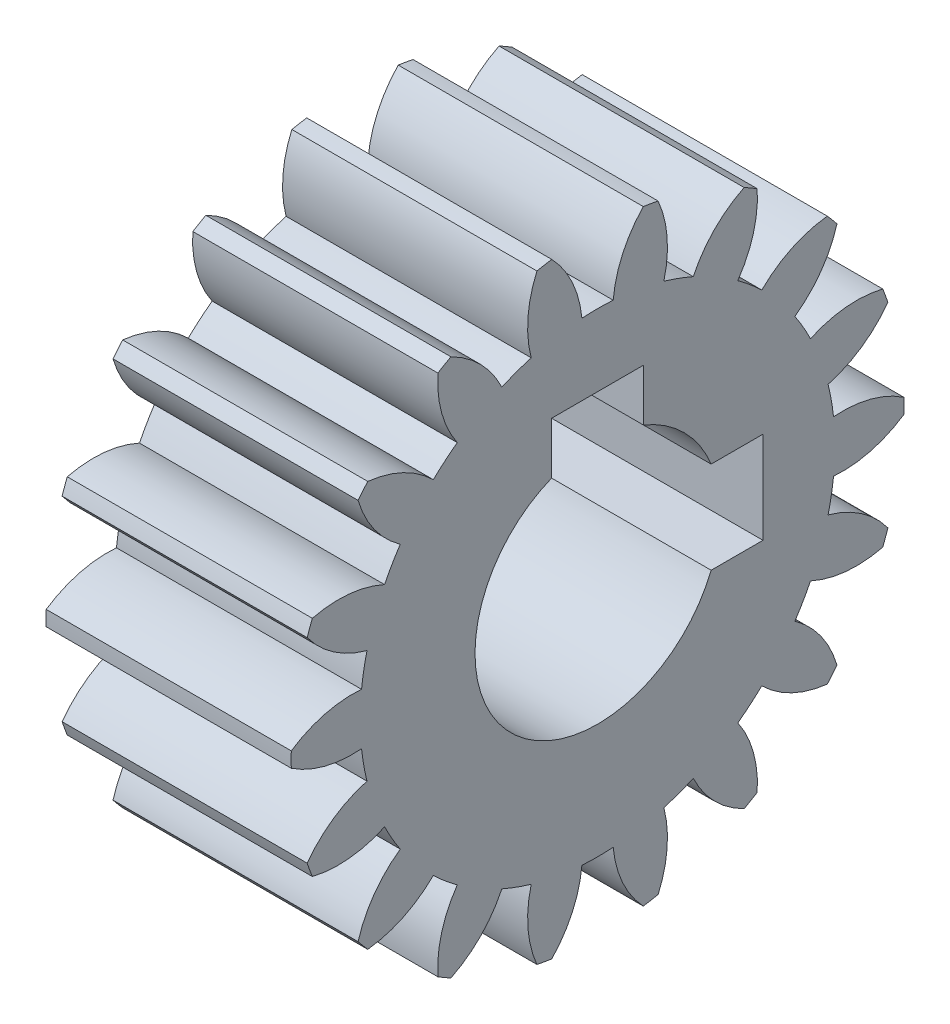
SolidWorks part; units mm, degrees
ref_plane "Plane1" through (0, 0, 0) normal (0, 0, 1) x (1, 0, 0)
ref_plane "Plane2" through (0, 0, 0) normal (0, 1, 0) x (1, 0, 0)
ref_plane "Plane3" through (0, 0, 0) normal (1, 0, 0) x (0, 0, -1)
sketch "HoldingSke" plane through (0, 0, 0) normal (0, 1, 0) x (1, 0, 0)
  line L0 (0, 0) -> (0.9511, -0.309)
  line L1 (-15, 0) -> (100, 0) construction
  line L2 (0, 0) -> (-2.1039, 2.3779)
  line L3 (0, 0) -> (-11.863, 4.5341)
  line L4 (0, 0) -> (8.2133, 2.6687)
  line L5 (0, 0) -> (-46.8476, -17.4728)
  line L6 (0, 0) -> (-6.6317, -4.4744)
  line L7 (-2.1039, 2.3779) -> (8.6586, 51.2059)
  line L8 (-76.2, 54.61) -> (-74.8, 54.61)
  line L9 (-71.009, 38.7566) -> (-53.1078, 45.2721)
  line L10 (-76.2, 71.12) -> (104.1128, 71.12)
  line L11 (0, 0) -> (-8, 0)
  line L12 (-76.2, 101.6) -> (-76.162, 101.6)
  line L13 (24.9733, 27.94) -> (52.9518, 28.4284)
  line L14 (24.9733, 27.94) -> (24.9743, 27.94)
  line L15 (24.9733, 27.94) -> (100.4006, 29.5858)
  line L16 (-63.627, -1) -> (-12.827, -1)
  circle A0 centre (0, 0) radius 4
  circle A1 centre (0, 0) radius 7.749
  circle A2 centre (0, 0) radius 37.5
  circle A3 centre (0, 0) radius 4
  dimension "MHD" = 15.498
  dimension "Hub_dia" = 75
  dimension "Bore" = 8
  dimension "MBD" = 8
  dimension "Num_teeth" = 18
  dimension "Pitch" = 1
  dimension "Overall_len" = 50
  dimension "Show_teeth" = 18
  dimension "Thickness" = 8
  dimension "OAL" = 50.0001
  dimension "T_dim" = 1.4
  dimension "Ap" = 20
  dimension "H" = 19.05
  dimension "Pitch_radius" = 180.3128
  dimension "Width" = 8
  dimension "Backlash" = 0.038
  dimension "Addendum_fac" = 1
  dimension "Dedendum_fac" = 1.25
  dimension "Clearance_fac" = 0.25
  dimension "Dedendum_add" = 0.001
  dimension "Module" = 1
sketch "BasProSke" plane through (0, 0, 0) normal (0, 1, 0) x (1, 0, 0)
  line L0 (-10, 0) -> (60, 0) construction
  line L1 (0, 0) -> (0, 10)
  line L2 (0, 0) -> (8, 0)
  line L3 (8, 0) -> (8, 10)
  line L4 (8, 10) -> (0, 10)
  dimension "Thickness" = 8
  dimension "Diameter" = 20
revolve "Base-Revolve" add sketch "BasProSke" angle 360 about L0
sketch "TooCutSke" plane through (0, 0, 0) normal (1, 0, 0) x (0, 0, -1)
  line L1 (0, 0) -> (0, 107) construction
  line L2 (0, 0) -> (-0.8509, 8.9597) construction
  line L3 (0, 0) -> (-3.1157, 17.6701) construction
  line L4 (-0.8509, 8.9597) -> (-1.5579, 8.835) construction
  arc A0 (0.5106, 7.7322) -> (-0.5106, 7.7322) centre (0, 0) ccw
  arc A1 (1.5152, 9.9102) -> (-1.5152, 9.9102) centre (0, 0) ccw
  circle A2 centre (0, 0) radius 9 construction
  circle A3 centre (0, 0) radius 8.4572 construction
  arc A4 (-0.5106, 7.7322) -> (-1.5152, 9.9102) centre (-4.0952, 7.3996) ccw
  arc A5 (1.5152, 9.9102) -> (0.5106, 7.7322) centre (4.0952, 7.3996) ccw
  dimension "Root_dia" = 15.498
  dimension "Overcut_dia" = 20.0508
  dimension "Pitch_dia" = 18
  dimension "Base_dia" = 16.9145
  dimension "Flank_rad" = 3.6
  dimension "Half_ang" = 10
  dimension "Half_CT" = 0.7179
extrude "ToothCut" cut sketch "TooCutSke" along normal through all
fillet "Breaks" [suppressed] radius 0.02
fillet "RootFillets" [suppressed] radius 0.251
pattern_circular "TeethCuts" count 18 every 20 about axis through (-10, 0, 0) along (1, 0, 0) of "ToothCut", "RootFillets", "Breaks"
sketch "HubNeaOneSke" plane through (0, 0, 0) normal (-1, 0, 0) x (0, 0, 1)
  circle A0 centre (0, 0) radius 7.749
  dimension "Diameter" = 15.498
extrude "HubNearOne" [suppressed] add sketch "HubNeaOneSke" along normal blind 42.0001
sketch "HubNeaBotSke" plane through (0, 0, 0) normal (-1, 0, 0) x (0, 0, 1)
  circle A0 centre (0, 0) radius 7.749
  dimension "Diameter" = 15.498
extrude "HubNearBoth" [suppressed] add sketch "HubNeaBotSke" along normal blind 21
ref_plane "FarPln" through (8, 0, 0) normal (1, 0, 0) x (0, 0, -1)
sketch "HubFarSke" plane through (8, 0, 0) normal (1, 0, 0) x (0, 0, -1)
  circle A0 centre (0, 0) radius 7.749
  dimension "Diameter" = 15.498
extrude "HubFar" [suppressed] add sketch "HubFarSke" along normal blind 21
sketch "BorSke" plane through (0, 0, 0) normal (1, 0, 0) x (0, 0, -1)
  circle A0 centre (0, 0) radius 4
  dimension "Diameter" = 8
extrude "Bore" cut sketch "BorSke" along normal mid plane 100.0001
sketch "KeySke" plane through (0, 0, 0) normal (1, 0, 0) x (0, 0, -1)
  line L0 (-1.5, 0) -> (-1.5, 5.4)
  line L1 (-1.5, 5.4) -> (1.5, 5.4)
  line L2 (1.5, 5.4) -> (1.5, 0)
  line L3 (0, 0) -> (0, 34) construction
  line L4 (-1.5, 0) -> (1.5, 0)
  dimension "Offset" = 5.4
  dimension "Width" = 3
extrude "Keyway" cut sketch "KeySke" along normal mid plane 100.0001
pattern_circular "Keyway2" count 2 every 90 about axis through (0, 0, 0) along (1, 0, 0) of "Keyway"
ref_plane "基准面1" through (4, 0, 0) normal (1, 0, 0) x (0, 0, -1)
sketch "草图1" plane through (4, 0, 0) normal (1, 0, 0) x (0, 0, -1)
  line L0 (0, 0) -> (4.981, 5.9361)
  line L1 (0, 0) -> (-4.981, 5.9361)
ref_plane "基准面2" through (0, 0, 0) normal (0, -0.6428, -0.766) x (-1, 0, 0)
ref_plane "基准面3" through (0, 0, 0) normal (0, 0.6428, -0.766) x (-1, 0, 0)
equation "' \"Module@HoldingSke\" = 6.35"
equation "' \"Num_teeth@HoldingSke\" = 12"
equation "' \"Ap@HoldingSke\" =  20"
equation "' \"Ap@HoldingSke\" = 20"
equation "' \"Width@HoldingSke\" = 0.5 * 25.4"
equation "' \"Hub_dia@HoldingSke\"= 1 * 25.4"
equation "' \"Hub_dia@HoldingSke\" = 1 * 25.4"
equation "' \"Overall_len@HoldingSke\" = 1.0 * 25.4"
equation "' \"Bore@HoldingSke\" = 0.75 * 25.4"
equation "' \"T_dim@HoldingSke\" = 0.1 * 25.4"
equation "' \"Width@KeySke\" = 0.25 * 25.4"
equation "' \"Show_teeth@HoldingSke\" = 13"
equation "' \"Backlash@HoldingSke\" = 0.009 * 25.4"
equation "' \"Addendum_fac@HoldingSke\" = 1.0"
equation "' \"Dedendum_fac@HoldingSke\" = 1.25"
equation "' \"Dedendum_add@HoldingSke\" = 0.00005 * 25.4"
equation "' \"Clearance_fac@HoldingSke\" = 0.25"
equation "\"Pitch@HoldingSke\" = 1 / \"Module@HoldingSke\""
equation "\"Overcut_dia@TooCutSke\" = (\"Num_teeth@HoldingSke\" + 2 * \"Addendum_fac@HoldingSke\") / \"Pitch@HoldingSke\" + 0.002 * 25.4"
equation "\"Pitch_dia@TooCutSke\" = \"Num_teeth@HoldingSke\" / \"Pitch@HoldingSke\""
equation "\"Base_dia@TooCutSke\" = \"Num_teeth@HoldingSke\" / \"Pitch@HoldingSke\" * cos((\"Ap@HoldingSke\"  * 3.14159265 / 180))"
equation "\"Root_dia@TooCutSke\" = (\"Num_teeth@HoldingSke\" + 2) / \"Pitch@HoldingSke\" - 2 * (\"Addendum_fac@HoldingSke\" + \"Dedendum_fac@HoldingSke\") / \"Pitch@HoldingSke\" - \"Dedendum_add@HoldingSke\" * 2"
equation "\"Half_ang@TooCutSke\" = 180 / \"Num_teeth@HoldingSke\""
equation "\"Half_CT@TooCutSke\" = \"Num_teeth@HoldingSke\" / \"Pitch@HoldingSke\" * sin((3.14159265 / 2 / \"Num_teeth@HoldingSke\")) / 2 - 7 * \"Backlash@HoldingSke\" / 4"
equation "\"Flank_rad@TooCutSke\" = \"Num_teeth@HoldingSke\" / \"Pitch@HoldingSke\" / 5"
equation "\"Radius@RootFillets\" = \"Clearance_fac@HoldingSke\" / \"Pitch@HoldingSke\" + \"Dedendum_add@HoldingSke\""
equation "\"Break_rad@Breaks\" = 0.02 / \"Pitch@HoldingSke\""
equation "\"Thickness@HoldingSke\" = \"Width@HoldingSke\""
equation "\"OAL@HoldingSke\" = \"Thickness@HoldingSke\""
equation "\"MHD@HoldingSke\" = (\"Num_teeth@HoldingSke\" + 2) / \"Pitch@HoldingSke\" - 2 * (\"Addendum_fac@HoldingSke\" + \"Dedendum_fac@HoldingSke\")  / \"Pitch@HoldingSke\" - \"Dedendum_add@HoldingSke\" * 2"
equation "\"MBD@HoldingSke\" = (\"Num_teeth@HoldingSke\" + 2) / \"Pitch@HoldingSke\" - 2 * (\"Addendum_fac@HoldingSke\" + \"Dedendum_fac@HoldingSke\")  / \"Pitch@HoldingSke\" - \"Dedendum_add@HoldingSke\" * 2 - 0.002 * 25.4"
equation "\"MHD@HoldingSke\" = ((sgn( \"MHD@HoldingSke\" - \"Hub_dia@HoldingSke\" )-1)*( \"MHD@HoldingSke\" - \"Hub_dia@HoldingSke\" ))/-2+ \"Hub_dia@HoldingSke\""
equation "\"MBD@HoldingSke\" = ((sgn( \"MBD@HoldingSke\" - \"Bore@HoldingSke\" )-1)*( \"MBD@HoldingSke\" - \"Bore@HoldingSke\" ))/-2+ \"Bore@HoldingSke\""
equation "\"OAL@HoldingSke\" = ((sgn( \"OAL@HoldingSke\" - \"Overall_len@HoldingSke\" )+1)*( \"OAL@HoldingSke\" - \"Overall_len@HoldingSke\" ))/2 + \"Overall_len@HoldingSke\" + 0.000002 * 25.4"
equation "\"Num_teeth@TeethCuts\" = int( \"Show_teeth@HoldingSke\" ) + 1"
equation "\"Num_teeth@TeethCuts\" = ((sgn( \"Num_teeth@TeethCuts\" - \"Num_teeth@HoldingSke\" )-1)*( \"Num_teeth@TeethCuts\" - \"Num_teeth@HoldingSke\" ))/-2+ \"Num_teeth@HoldingSke\""
equation "\"Num_teeth@TeethCuts\" = ((sgn( \"Num_teeth@TeethCuts\" - 2.0)+1)*( \"Num_teeth@TeethCuts\" - 2.0))/2 +2.0"
equation "\"Angle@TeethCuts\" = 360.0 / \"Num_teeth@HoldingSke\""
equation "\"Diameter@BasProSke\" = (\"Num_teeth@HoldingSke\" + 2 * \"Addendum_fac@HoldingSke\") / \"Pitch@HoldingSke\""
equation "\"Thickness@BasProSke\"  = \"Thickness@HoldingSke\""
equation "' \"Fillet_rad@BasProSke\" =  \"Thickness@HoldingSke\" * 0.05"
equation "' \"Fillet_rad@BasProSke\" = \"Thickness@HoldingSke\" * 0.05"
equation "\"MHD@HoldingSke\" = ((sgn( \"MHD@HoldingSke\" - \"Root_dia@TooCutSke\" )-1)*( \"MHD@HoldingSke\" - \"Root_dia@TooCutSke\" ))/-2+ \"Root_dia@TooCutSke\""
equation "\"Diameter@HubNeaOneSke\" = \"MHD@HoldingSke\""
equation "\"Length@HubNearOne\" = \"OAL@HoldingSke\" - \"Thickness@BasProSke\""
equation "\"Diameter@HubNeaBotSke\" = \"MHD@HoldingSke\""
equation "\"Length@HubNearBoth\" = ( \"OAL@HoldingSke\" - \"Thickness@BasProSke\" ) / 2.0"
equation "\"Thickness@FarPln\" = \"Thickness@BasProSke\""
equation "\"Diameter@HubFarSke\" = \"MHD@HoldingSke\""
equation "\"Length@HubFar\" = ( \"OAL@HoldingSke\" - \"Thickness@BasProSke\" ) / 2.0"
equation "\"Diameter@BorSke\" = \"MBD@HoldingSke\""
equation "\"D1@Bore\" = \"OAL@HoldingSke\" * 2.0"
equation "\"D1@Keyway\" = \"OAL@HoldingSke\" * 2.0"
equation "\"Offset@KeySke\" = \"T_dim@HoldingSke\" + \"MBD@HoldingSke\" / 2.0"
